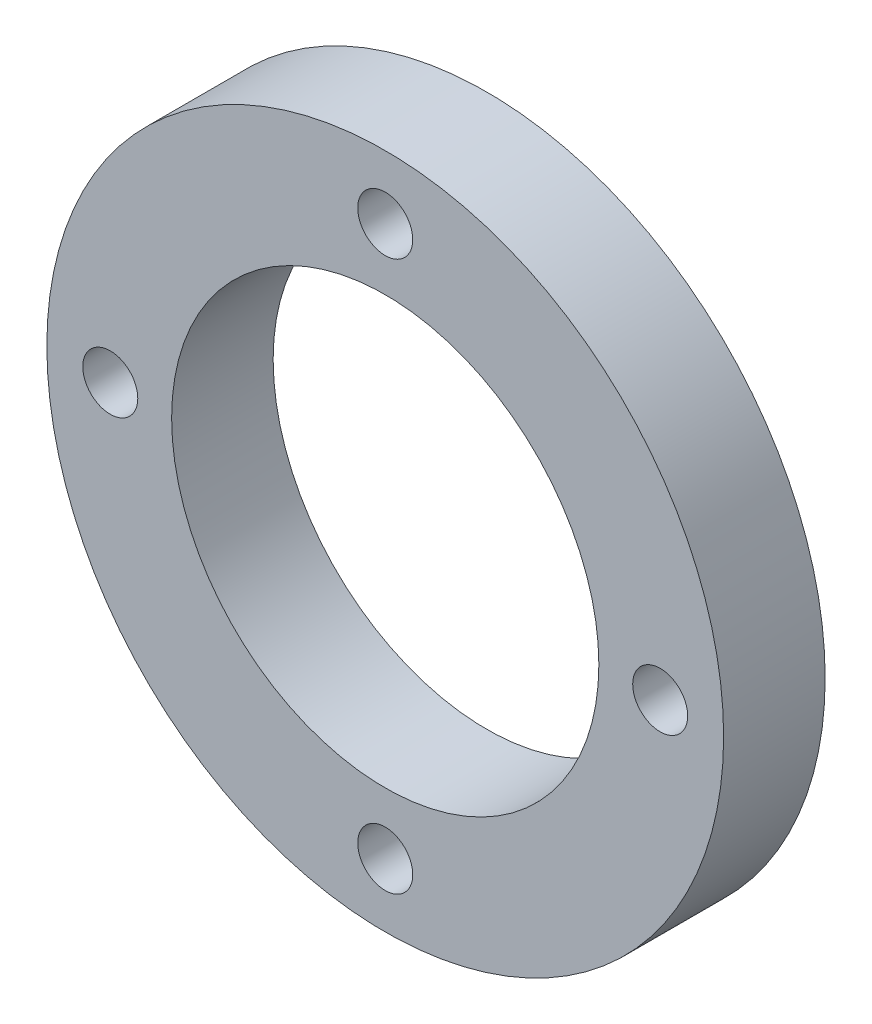
SolidWorks part; units mm, degrees
material "1060 Alloy"
ref_plane "Front Plane" through (0, 0, 0) normal (0, 0, 1) x (1, 0, 0)
ref_plane "Top Plane" through (0, 0, 0) normal (0, 1, 0) x (1, 0, 0)
ref_plane "Right Plane" through (0, 0, 0) normal (1, 0, 0) x (0, 0, -1)
sketch "Sketch1" plane through (0, 0, 0) normal (0, 0, 1) x (1, 0, 0)
  line L0 (0, 40) -> (0, -40) construction
  line L1 (40, 0) -> (-40, 0) construction
  circle A0 centre (0, 0) radius 40
  circle A1 centre (0, 0) radius 25.25
  circle A2 centre (0, 0) radius 32.5 construction
  circle A3 centre (-32.5, 0) radius 3.25
  circle A4 centre (0, 32.5) radius 3.25
  circle A5 centre (0, -32.5) radius 3.25
  circle A6 centre (32.5, 0) radius 3.25
  dimension "D1" = 50.5
  dimension "D2" = 80
  dimension "D3" = 6.5
  dimension "D4" = 65
extrude "Boss-Extrude1" add sketch "Sketch1" along normal mid plane 12
